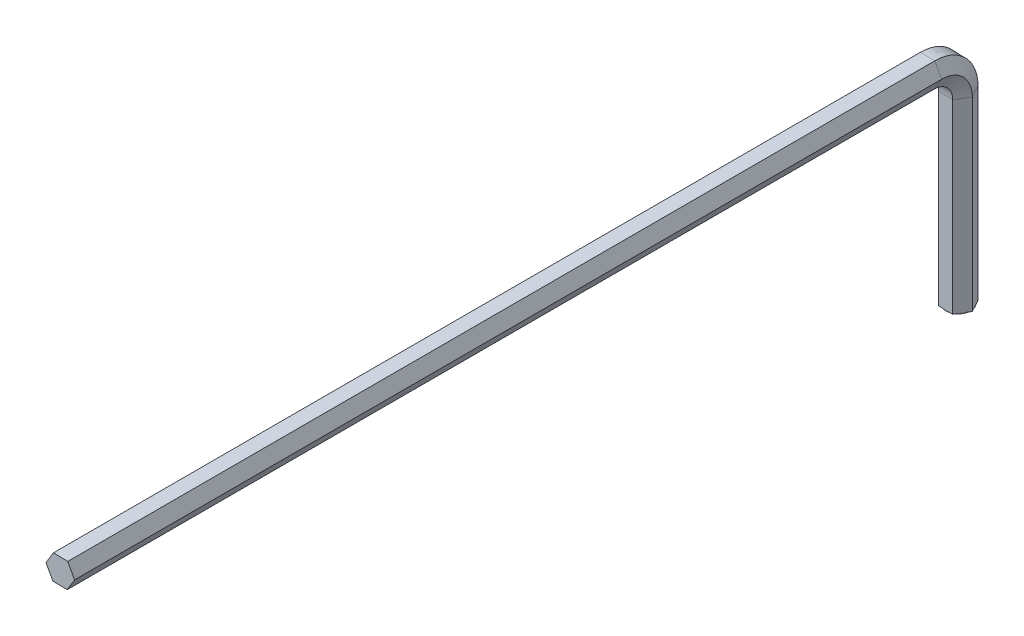
SolidWorks part; units mm, degrees
material "1060 Alloy"
ref_plane "Front Plane" through (0, 0, 0) normal (1, 0, 0) x (0, 1, 0)
ref_plane "Top Plane" through (0, 0, 0) normal (0, 0, 1) x (0, 1, 0)
ref_plane "Right Plane" through (0, 0, 0) normal (0, 1, 0) x (-1, 0, 0)
sketch3d "3DSketch1"
  line L0 (0, 0, 0) -> (0, 30, 0)
  line L1 (0, 35, 5) -> (0, 35, 145)
  arc A0 (0, 35, 5) -> (0, 30, 0) centre (0, 30, 5) ccw
  point P6 (0, 35, 0)
  point P7 (-5, 30, 5)
  dimension "D1" = 5
  dimension "D2" = 35
  dimension "D3" = 145
sketch "Sketch1" plane through (0, 0, 0) normal (0, 1, 0) x (-1, 0, 0)
  line L0 (2.3089, -0.0493) -> (1.1971, 1.9749)
  line L1 (-1.1117, 2.0242) -> (-2.3089, 0.0493)
  line L2 (-2.3089, 0.0493) -> (-1.1971, -1.9749)
  line L3 (-1.1971, -1.9749) -> (1.1117, -2.0242)
  line L4 (1.1117, -2.0242) -> (2.3089, -0.0493)
  line L5 (1.1971, 1.9749) -> (-1.1117, 2.0242)
  circle A1 centre (0, 0) radius 2 construction
  dimension "D1" = 4
sweep "Sweep1" add profiles "Sketch1" path "3DSketch1"
sketch "Sketch2" plane through (0, 0, 0) normal (0, -1, 0) x (1, 0, 0)
  circle A0 centre (0, 0) radius 2
extrude "Boss-Extrude1" add sketch "Sketch2" along normal blind 0.1
